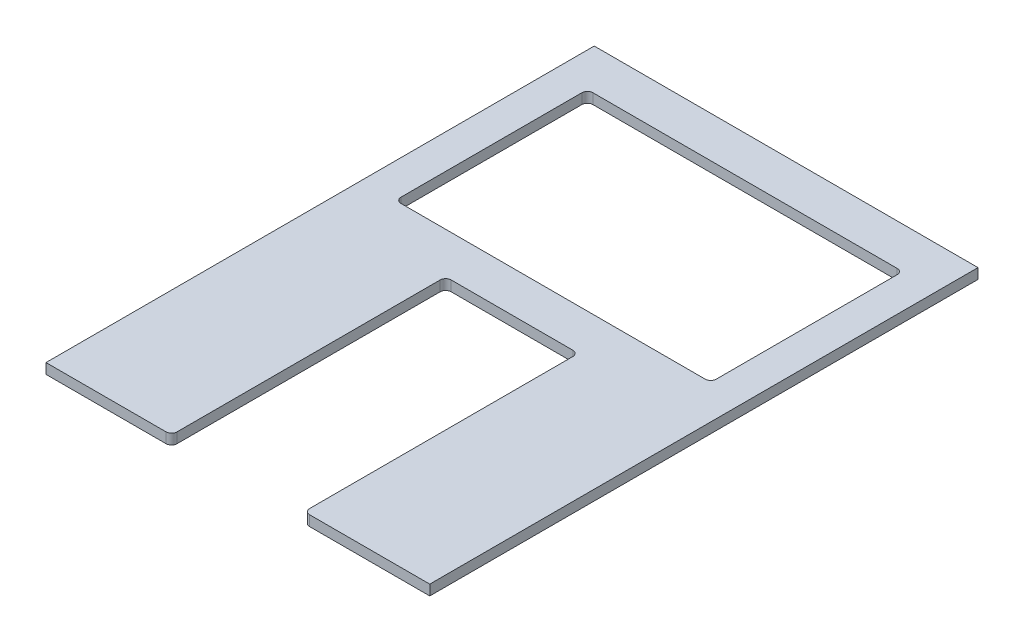
SolidWorks part; units mm, degrees
material "Delrin 2700 NC010, Low Viscosity Acetal Copolymer (SS)"
ref_plane "Front Plane"
ref_plane "Top Plane" through (0, 0, 0) normal (0, 1, 0) x (1, 0, 0)
ref_plane "Right Plane" through (0, 0, 0) normal (1, 0, 0) x (0, 0, -1)
sketch "Sketch1" plane through (0, 0, 0) normal (0, 1, 0) x (1, 0, 0)
  line L0 (-30.734, -127) -> (-30.734, 0)
  line L1 (88.9, 127) -> (-88.9, 127)
  line L2 (88.9, 127) -> (88.9, -127)
  line L3 (88.9, -127) -> (30.734, -127)
  line L4 (-88.9, 127) -> (-88.9, -127)
  line L5 (88.9, 127) -> (-88.9, -127) construction
  line L6 (88.9, -127) -> (-88.9, 127) construction
  line L7 (-30.734, 0) -> (30.734, 0)
  line L8 (30.734, 0) -> (30.734, -127)
  line L9 (-30.734, -127) -> (-88.9, -127)
  line L10 (0, 0) -> (0, 127) construction
  line L12 (73.025, 107.95) -> (-73.025, 107.95)
  line L13 (73.025, 107.95) -> (73.025, 19.05)
  line L14 (73.025, 19.05) -> (-73.025, 19.05)
  line L15 (-73.025, 107.95) -> (-73.025, 19.05)
  line L16 (73.025, 107.95) -> (-73.025, 19.05) construction
  line L17 (73.025, 19.05) -> (-73.025, 107.95) construction
  point P0 (0, 0)
  point P12 (0, 63.5)
  dimension "D1" = 254
  dimension "D2" = 177.8
  dimension "D3" = 61.468
  dimension "D4" = 58.166
  dimension "D5" = 127
  dimension "D6" = 88.9
  dimension "D7" = 146.05
extrude "Boss-Extrude1" add sketch "Sketch1" along normal blind 4.7625
fillet "Fillet1" radius 2.54 8 edges at (30.734, 2.3813, 127) (-30.734, 2.3813, 127) (-30.734, 2.3813, 0) (30.734, 2.3813, 0) (-73.025, 2.3813, -19.05) (73.025, 2.3813, -19.05) (73.025, 2.3813, -107.95) (-73.025, 2.3813, -107.95)
